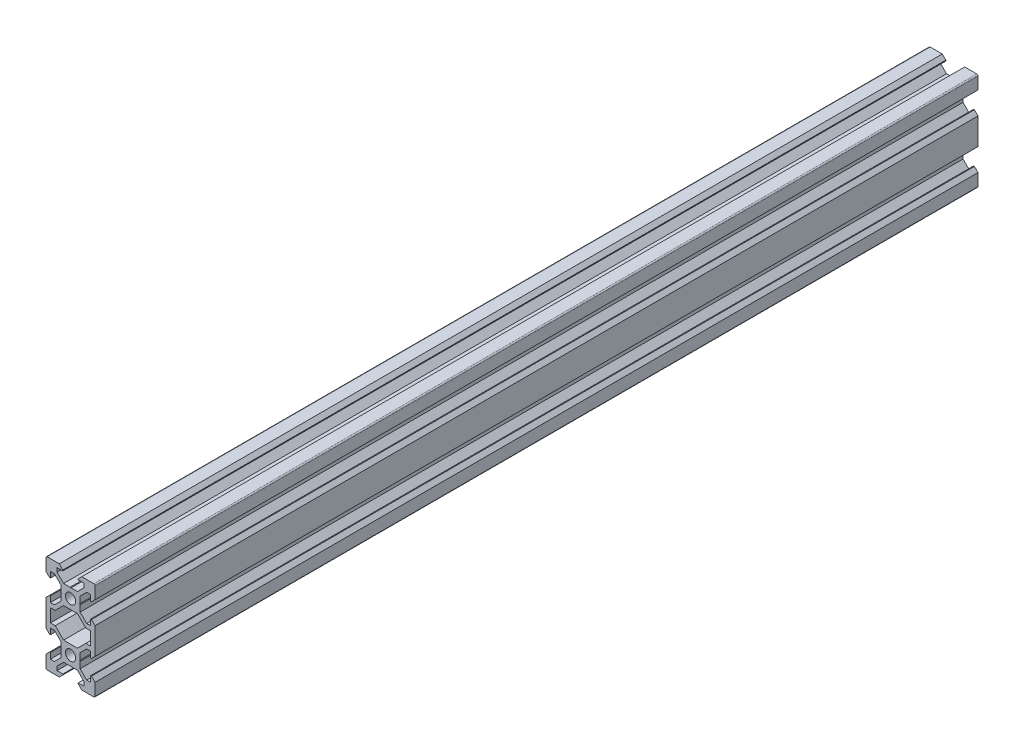
SolidWorks part; units mm, degrees
material "6061-T6 (SS)"
ref_plane "Front Plane" through (0, 0, 0) normal (0, 0, 1) x (1, 0, 0)
ref_plane "Top Plane" through (0, 0, 0) normal (0, 1, 0) x (1, 0, 0)
ref_plane "Right Plane" through (0, 0, 0) normal (1, 0, 0) x (0, 0, -1)
sketch "Sketch1" plane through (0, 0, 0) normal (0, 0, 1) x (1, 0, 0)
  line L0 (0, 0) -> (10, 0) construction
  line L1 (9.5, -20) -> (-9.5, -20)
  line L2 (10, -19.5) -> (10, 19.5)
  line L3 (9.5, 20) -> (-9.5, 20)
  line L4 (-10, -19.5) -> (-10, 19.5)
  line L5 (10, -20) -> (-10, 20) construction
  line L6 (10, 20) -> (-10, -20) construction
  circle A0 centre (0, 10) radius 2.1
  circle A1 centre (0, -10) radius 2.1
  arc A2 (-9.5, -20) -> (-10, -19.5) centre (-9.5, -19.5) cw
  arc A3 (9.5, -20) -> (10, -19.5) centre (9.5, -19.5) ccw
  arc A4 (10, 19.5) -> (9.5, 20) centre (9.5, 19.5) ccw
  arc A5 (-9.5, 20) -> (-10, 19.5) centre (-9.5, 19.5) ccw
  point P0 (0, 0)
  line B0 (0, 10) -> (0, 20) construction
  line B1 (0, 13.69) -> (-0.21, 13.9)
  line B2 (-0.21, 13.9) -> (-2.8393, 13.9)
  line B3 (-2.8393, 13.9) -> (-5.5, 16.5607)
  line B4 (-5.5, 16.5607) -> (-5.5, 18.2)
  line B5 (-5.5, 18.2) -> (-3.125, 18.2)
  line B6 (-3.125, 18.2) -> (-3.125, 18.545)
  line B7 (-3.125, 18.545) -> (-4.58, 20)
  line B8 (-4.58, 20) -> (4.58, 20)
  line B9 (0, 10) -> (-5.9132, 15.9132) construction
  line B10 (3.125, 18.545) -> (4.58, 20)
  line B11 (3.125, 18.2) -> (3.125, 18.545)
  line B12 (5.5, 18.2) -> (3.125, 18.2)
  line B13 (5.5, 16.5607) -> (5.5, 18.2)
  line B14 (2.8393, 13.9) -> (5.5, 16.5607)
  line B15 (0.21, 13.9) -> (2.8393, 13.9)
  line B16 (0, 13.69) -> (0.21, 13.9)
  line B17 (0, 10) -> (-10, 10) construction
  line B18 (-3.69, 10) -> (-3.9, 9.79)
  line B19 (-3.9, 9.79) -> (-3.9, 7.1607)
  line B20 (-3.9, 7.1607) -> (-6.5607, 4.5)
  line B21 (-6.5607, 4.5) -> (-8.2, 4.5)
  line B22 (-8.2, 4.5) -> (-8.2, 6.875)
  line B23 (-8.2, 6.875) -> (-8.545, 6.875)
  line B24 (-8.545, 6.875) -> (-10, 5.42)
  line B25 (-10, 5.42) -> (-10, 14.58)
  line B26 (0, 10) -> (-5.9132, 4.0868) construction
  line B27 (-8.545, 13.125) -> (-10, 14.58)
  line B28 (-8.2, 13.125) -> (-8.545, 13.125)
  line B29 (-8.2, 15.5) -> (-8.2, 13.125)
  line B30 (-6.5607, 15.5) -> (-8.2, 15.5)
  line B31 (-3.9, 12.8393) -> (-6.5607, 15.5)
  line B32 (-3.9, 10.21) -> (-3.9, 12.8393)
  line B33 (-3.69, 10) -> (-3.9, 10.21)
  line B34 (0, -10) -> (-10, -10) construction
  line B35 (-3.69, -10) -> (-3.9, -10.21)
  line B36 (-3.9, -10.21) -> (-3.9, -12.8393)
  line B37 (-3.9, -12.8393) -> (-6.5607, -15.5)
  line B38 (-6.5607, -15.5) -> (-8.2, -15.5)
  line B39 (-8.2, -15.5) -> (-8.2, -13.125)
  line B40 (-8.2, -13.125) -> (-8.545, -13.125)
  line B41 (-8.545, -13.125) -> (-10, -14.58)
  line B42 (-10, -14.58) -> (-10, -5.42)
  line B43 (0, -10) -> (-5.9132, -15.9132) construction
  line B44 (-8.545, -6.875) -> (-10, -5.42)
  line B45 (-8.2, -6.875) -> (-8.545, -6.875)
  line B46 (-8.2, -4.5) -> (-8.2, -6.875)
  line B47 (-6.5607, -4.5) -> (-8.2, -4.5)
  line B48 (-3.9, -7.1607) -> (-6.5607, -4.5)
  line B49 (-3.9, -9.79) -> (-3.9, -7.1607)
  line B50 (-3.69, -10) -> (-3.9, -9.79)
  line B51 (0, -10) -> (0, -20) construction
  line B52 (0, -13.69) -> (0.21, -13.9)
  line B53 (0.21, -13.9) -> (2.8393, -13.9)
  line B54 (2.8393, -13.9) -> (5.5, -16.5607)
  line B55 (5.5, -16.5607) -> (5.5, -18.2)
  line B56 (5.5, -18.2) -> (3.125, -18.2)
  line B57 (3.125, -18.2) -> (3.125, -18.545)
  line B58 (3.125, -18.545) -> (4.58, -20)
  line B59 (4.58, -20) -> (-4.58, -20)
  line B60 (0, -10) -> (5.9132, -15.9132) construction
  line B61 (-3.125, -18.545) -> (-4.58, -20)
  line B62 (-3.125, -18.2) -> (-3.125, -18.545)
  line B63 (-5.5, -18.2) -> (-3.125, -18.2)
  line B64 (-5.5, -16.5607) -> (-5.5, -18.2)
  line B65 (-2.8393, -13.9) -> (-5.5, -16.5607)
  line B66 (-0.21, -13.9) -> (-2.8393, -13.9)
  line B67 (0, -13.69) -> (-0.21, -13.9)
  line B68 (0, -10) -> (10, -10) construction
  line B69 (3.69, -10) -> (3.9, -9.79)
  line B70 (3.9, -9.79) -> (3.9, -7.1607)
  line B71 (3.9, -7.1607) -> (6.5607, -4.5)
  line B72 (6.5607, -4.5) -> (8.2, -4.5)
  line B73 (8.2, -4.5) -> (8.2, -6.875)
  line B74 (8.2, -6.875) -> (8.545, -6.875)
  line B75 (8.545, -6.875) -> (10, -5.42)
  line B76 (10, -5.42) -> (10, -14.58)
  line B77 (0, -10) -> (5.9132, -4.0868) construction
  line B78 (8.545, -13.125) -> (10, -14.58)
  line B79 (8.2, -13.125) -> (8.545, -13.125)
  line B80 (8.2, -15.5) -> (8.2, -13.125)
  line B81 (6.5607, -15.5) -> (8.2, -15.5)
  line B82 (3.9, -12.8393) -> (6.5607, -15.5)
  line B83 (3.9, -10.21) -> (3.9, -12.8393)
  line B84 (3.69, -10) -> (3.9, -10.21)
  line B85 (0, 10) -> (10, 10) construction
  line B86 (3.69, 10) -> (3.9, 10.21)
  line B87 (3.9, 10.21) -> (3.9, 12.8393)
  line B88 (3.9, 12.8393) -> (6.5607, 15.5)
  line B89 (6.5607, 15.5) -> (8.2, 15.5)
  line B90 (8.2, 15.5) -> (8.2, 13.125)
  line B91 (8.2, 13.125) -> (8.545, 13.125)
  line B92 (8.545, 13.125) -> (10, 14.58)
  line B93 (10, 14.58) -> (10, 5.42)
  line B94 (0, 10) -> (5.9132, 15.9132) construction
  line B95 (8.545, 6.875) -> (10, 5.42)
  line B96 (8.2, 6.875) -> (8.545, 6.875)
  line B97 (8.2, 4.5) -> (8.2, 6.875)
  line B98 (6.5607, 4.5) -> (8.2, 4.5)
  line B99 (3.9, 7.1607) -> (6.5607, 4.5)
  line B100 (3.9, 9.79) -> (3.9, 7.1607)
  line B101 (3.69, 10) -> (3.9, 9.79)
  line B102 (-8.2, -2.7) -> (-8.2, 2.7)
  line B103 (-8.2, 2.7) -> (-6.2393, 2.7)
  line B104 (-6.2393, 2.7) -> (-2.8393, 6.1)
  line B105 (-2.8393, 6.1) -> (2.8393, 6.1)
  line B106 (0, 6.1) -> (0, 0) construction
  line B107 (0, 0) -> (-8.2, 0) construction
  line B108 (6.2393, 2.7) -> (2.8393, 6.1)
  line B109 (8.2, 2.7) -> (6.2393, 2.7)
  line B110 (8.2, -2.7) -> (8.2, 2.7)
  line B111 (8.2, -2.7) -> (6.2393, -2.7)
  line B112 (6.2393, -2.7) -> (2.8393, -6.1)
  line B113 (-2.8393, -6.1) -> (2.8393, -6.1)
  line B114 (-6.2393, -2.7) -> (-2.8393, -6.1)
  line B115 (-8.2, -2.7) -> (-6.2393, -2.7)
  line B116 (0, 6.1) -> (0, 10) construction
  line B117 (0, 10) -> (-5.0927, 4.9073) construction
  dimension "D4" = 4.2
  dimension "D5" = 0.5
  dimension "D1" = 20
  dimension "D2" = 40
  dimension "D3" = 20
sketch_block_instance "V Slot 1-4"
sketch_block "V Slot 1" parameters "D1"=10, "D2"=11, "D3"=4.3, "D4"=1.8, "D5"=0.21, "D6"=45, "D7"=9.16, "D8"=1.5, "D9"=6.25
sketch_block_instance "V Slot 1-5"
sketch_block_instance "V Slot 1-6"
sketch_block_instance "V Slot 1-7"
sketch_block_instance "V Slot 1-8"
sketch_block_instance "V Slot 1-9"
sketch_block_instance "Center Cutout 1-1"
sketch_block "Center Cutout 1" parameters "D1"=5.4, "D2"=12.2, "D3"=8.2, "D4"=45, "D5"=10, "D6"=1.5
extrude "Boss-Extrude1" add sketch "Sketch1" along normal blind 360 contours B101 B86 B87 B88 B89 B90 B91 B92 L2 A4 L3 B10 B11 B12 B13 B14 B15 B16 B1 B2 B3 B4 B5 B6 B7 A5 L4 B27 B28 B29 B30 B31 B32 B33 B18 B19 B20 B21 B22 B23 B24 B44 B45 B46 B47 B48 B49 B50 B35
ref_plane "Plane1" through (0, 0, 180) normal (0, 0, 1) x (1, 0, 0)
